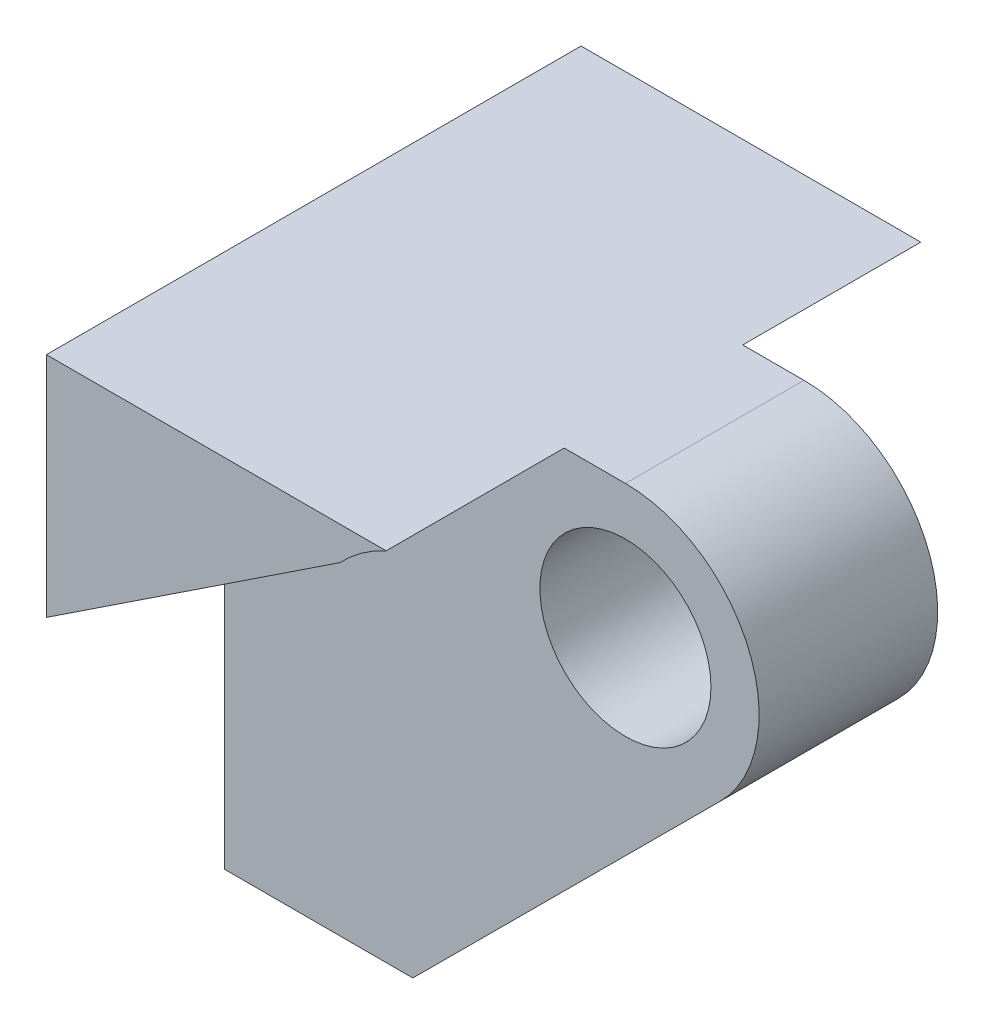
SolidWorks part; units mm, degrees
ref_plane "Front Plane" through (0, 0, 0) normal (0, 0, 1) x (1, 0, 0)
ref_plane "Top Plane" through (0, 0, 0) normal (0, 1, 0) x (1, 0, 0)
ref_plane "Right Plane" through (0, 0, 0) normal (1, 0, 0) x (0, 0, -1)
sketch "Sketch1" plane through (0, 0, 0) normal (0, 0, 1) x (1, 0, 0)
  line L0 (0, 2.5) -> (-7.5, 2.5)
  line L1 (-3.977, -7.5) -> (1.7658, -1.7697)
  line L2 (-7.5, 2.5) -> (-7.5, -7.5)
  line L3 (-7.5, -7.5) -> (-3.977, -7.5)
  circle A0 centre (0, 0) radius 1.6
  arc A1 (1.7658, -1.7697) -> (0, 2.5) centre (0, 0) ccw
  dimension "D1" = 3.2
  dimension "D2" = 5
  dimension "D3" = 7.5
  dimension "D4" = 10
  dimension "D5" = 8.1127
extrude "Boss-Extrude1" add sketch "Sketch1" along normal blind 5
sketch "Sketch4" plane through (0, 0, 5) normal (0, 0, 1) x (1, 0, 0)
  line L0 (1.943, -1.946) -> (-3.8233, -7.9105)
  line L1 (-3.8233, -7.9105) -> (-8.5102, -7.9105)
  line L2 (-8.5102, -7.9105) -> (-8.5102, -2.4242)
  line L3 (-8.5102, -2.4242) -> (-2.0105, 1.8762)
  arc A0 (1.943, -1.946) -> (-2.0105, 1.8762) centre (0, 0) ccw
  dimension "D1" = 5.5
extrude "Cut-Extrude2" cut sketch "Sketch4" against normal blind 3.33
sketch "Sketch5" [suppressed] plane through (0, 0, 0) normal (0, 0, -1) x (-1, 0, 0)
  circle A0 centre (0, 0) radius 2.75
  dimension "D1" = 5.5
extrude "Cut-Extrude3" [suppressed] cut sketch "Sketch5" against normal blind 1.665
mirror "Mirror1" about plane through (0, 0, 0) normal (0, 0, 1) of bodies 103 104
